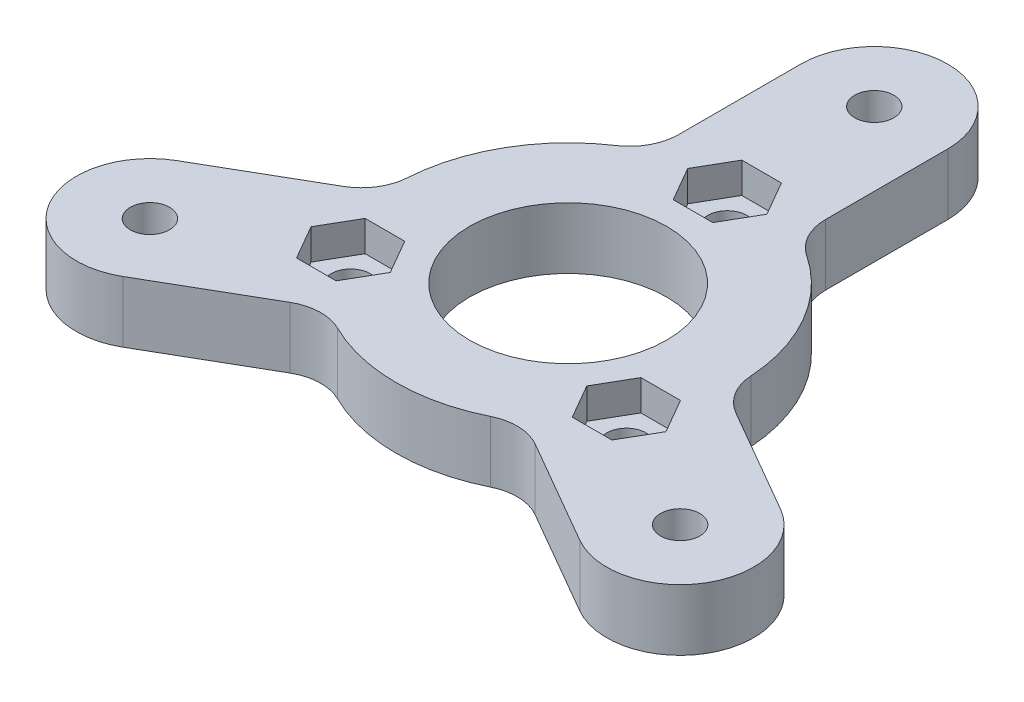
SolidWorks part; units mm, degrees
ref_plane "Front Plane" through (0, 0, 0) normal (0, 0, 1) x (1, 0, 0)
ref_plane "Top Plane" through (0, 0, 0) normal (0, 1, 0) x (1, 0, 0)
ref_plane "Right Plane" through (0, 0, 0) normal (1, 0, 0) x (0, 0, -1)
sketch "Sketch1" plane through (0, 0, 0) normal (0, 1, 0) x (1, 0, 0)
  line L0 (0, 0) -> (0, 9.0907) construction
  line L1 (0, 0) -> (7.1459, -4.1257) construction
  line L2 (0, 0) -> (-8.3205, -4.8039) construction
  line L3 (24.6506, -7.3038) -> (16.0135, -2.3172)
  line L4 (18.6506, -17.6962) -> (10.0135, -12.7095)
  line L5 (-18.6506, -17.6962) -> (-10.0135, -12.7095)
  line L6 (-24.6506, -7.3038) -> (-16.0135, -2.3172)
  line L7 (-6, 25) -> (-6, 15.0267)
  line L8 (6, 25) -> (6, 15.0267)
  circle A0 centre (0, 0) radius 8.05
  arc A1 (14.0216, 0.8927) -> (7.7839, 11.6967) centre (0, 0) ccw
  circle A2 centre (0, 25) radius 1.6
  circle A3 centre (0, 0) radius 25 construction
  circle A4 centre (21.6506, -12.5) radius 1.6
  circle A5 centre (-21.6506, -12.5) radius 1.6
  arc A6 (18.6506, -17.6962) -> (24.6506, -7.3038) centre (21.6506, -12.5) ccw
  arc A7 (-24.6506, -7.3038) -> (-18.6506, -17.6962) centre (-21.6506, -12.5) ccw
  arc A8 (6, 25) -> (-6, 25) centre (0, 25) ccw
  arc A9 (-7.7839, 11.6967) -> (-14.0216, 0.8927) centre (0, 0) ccw
  arc A10 (-6.2377, -12.5894) -> (6.2377, -12.5894) centre (0, 0) ccw
  arc A11 (-16.0135, -2.3172) -> (-14.0216, 0.8927) centre (-18.0135, 1.1469) ccw
  arc A12 (-10.0135, -12.7095) -> (-6.2377, -12.5894) centre (-8.0135, -16.1736) cw
  arc A13 (10.0135, -12.7095) -> (6.2377, -12.5894) centre (8.0135, -16.1736) ccw
  arc A14 (16.0135, -2.3172) -> (14.0216, 0.8927) centre (18.0135, 1.1469) cw
  arc A15 (6, 15.0267) -> (7.7839, 11.6967) centre (10, 15.0267) ccw
  arc A16 (-6, 15.0267) -> (-7.7839, 11.6967) centre (-10, 15.0267) cw
  point P36 (0, 0)
  dimension "D3" = 16.1
  dimension "D4" = 6
  dimension "D5" = 50
  dimension "D6" = 3.2
  dimension "D7" = 12
  dimension "D9" = 4
  dimension "D1" = 120
  dimension "D2" = 120
  dimension "D8" = 3
extrude "Boss-Extrude1" add sketch "Sketch1" along normal blind 5
sketch "Sketch3" plane through (0, 5, 0) normal (0, 1, 0) x (1, 0, 0)
  line L0 (0, 0) -> (0, 25) construction
  line L1 (0, 0) -> (21.6506, -12.5) construction
  line L2 (0, 0) -> (-21.6506, -12.5) construction
  line L4 (1.6166, 15.8) -> (-1.6166, 15.8)
  line L5 (-1.6166, 15.8) -> (-3.2332, 13)
  line L6 (-3.2332, 13) -> (-1.6166, 10.2)
  line L7 (-1.6166, 10.2) -> (1.6166, 10.2)
  line L8 (1.6166, 10.2) -> (3.2332, 13)
  line L9 (3.2332, 13) -> (1.6166, 15.8)
  line L10 (-8.0252, -6.5) -> (-9.6417, -3.7)
  line L11 (-9.6417, -3.7) -> (-12.8749, -3.7)
  line L12 (-12.8749, -3.7) -> (-14.4915, -6.5)
  line L13 (-14.4915, -6.5) -> (-12.8749, -9.3)
  line L14 (-12.8749, -9.3) -> (-9.6417, -9.3)
  line L15 (-9.6417, -9.3) -> (-8.0252, -6.5)
  line L16 (14.4915, -6.5) -> (12.8749, -3.7)
  line L17 (12.8749, -3.7) -> (9.6417, -3.7)
  line L18 (9.6417, -3.7) -> (8.0252, -6.5)
  line L19 (8.0252, -6.5) -> (9.6417, -9.3)
  line L20 (9.6417, -9.3) -> (12.8749, -9.3)
  line L21 (12.8749, -9.3) -> (14.4915, -6.5)
  circle A0 centre (0, 13) radius 2.8 construction
  circle A1 centre (-11.2583, -6.5) radius 2.8 construction
  circle A2 centre (11.2583, -6.5) radius 2.8 construction
  circle A3 centre (0, 0) radius 13 construction
  dimension "D1" = 26
  dimension "D2" = 5.6
extrude "Cut-Extrude1" cut sketch "Sketch3" against normal blind 2.5
sketch "Sketch4" plane through (0, 2.5, 0) normal (0, 1, 0) x (1, 0, 0)
  circle A0 centre (0, 13) radius 1.6
  circle A1 centre (11.2583, -6.5) radius 1.6
  circle A2 centre (-11.2583, -6.5) radius 1.6
  dimension "D1" = 3.2
extrude "Cut-Extrude2" cut sketch "Sketch4" against normal up to next
